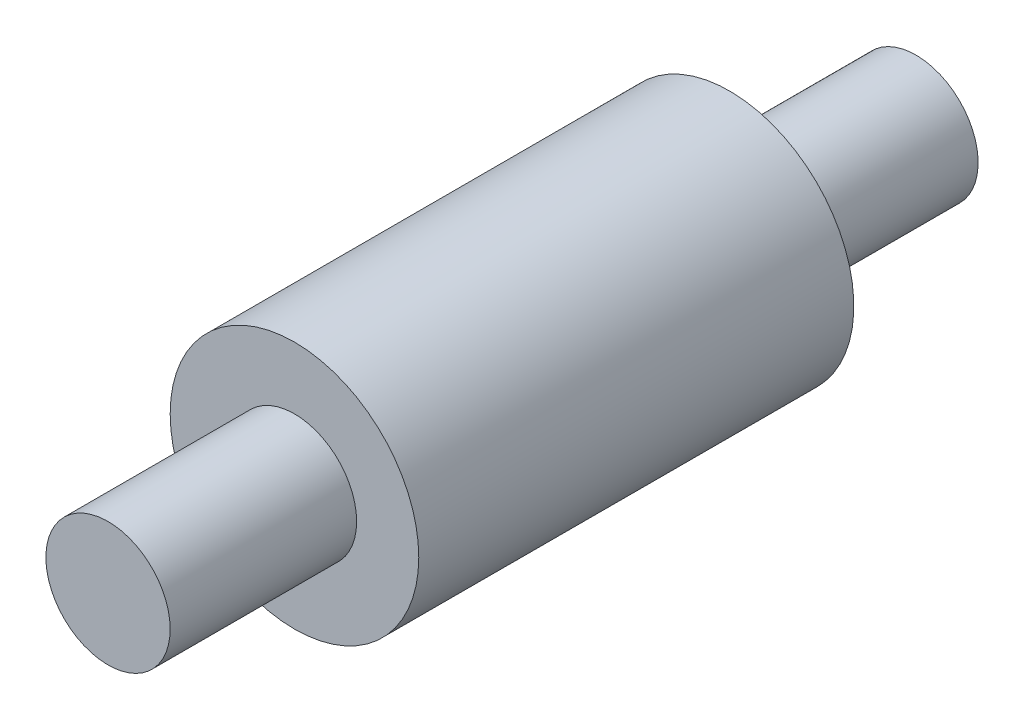
SolidWorks part; units mm, degrees
material "1023 Carbon Steel Sheet (SS)"
ref_plane "Front Plane" through (0, 0, 0) normal (0, 0, 1) x (1, 0, 0)
ref_plane "Top Plane" through (0, 0, 0) normal (0, 1, 0) x (1, 0, 0)
ref_plane "Right Plane" through (0, 0, 0) normal (1, 0, 0) x (0, 0, -1)
sketch "Sketch2" plane through (0, 0, 0) normal (0, 0, 1) x (1, 0, 0)
  circle A0 centre (0, 0) radius 20
extrude "Boss-Extrude4" add sketch "Sketch2" along normal blind 130
sketch "Sketch3" plane through (0, 0, 130) normal (0, 0, 1) x (1, 0, 0)
  circle A0 centre (0, 0) radius 10
extrude "Cut-Extrude1" cut sketch "Sketch3" against normal blind 30 flip side to cut
sketch "Sketch4" plane through (0, 0, 0) normal (0, 0, -1) x (-1, 0, 0)
  circle A0 centre (0, 0) radius 10
extrude "Cut-Extrude2" cut sketch "Sketch4" against normal blind 30 flip side to cut
